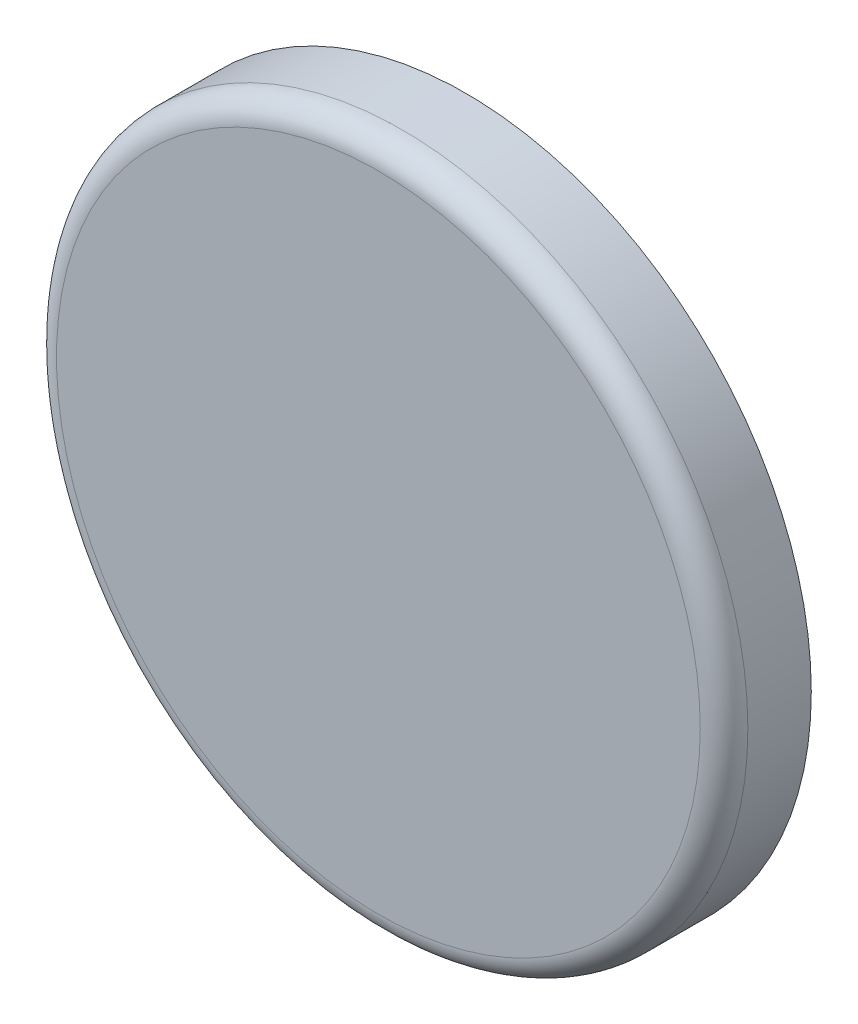
SolidWorks part; units mm, degrees
ref_plane "Alzado" through (0, 0, 0) normal (0, 0, 1) x (1, 0, 0)
ref_plane "Planta" through (0, 0, 0) normal (0, 1, 0) x (1, 0, 0)
ref_plane "Vista lateral" through (0, 0, 0) normal (1, 0, 0) x (0, 0, -1)
sketch "Croquis1" plane through (0, 0, 0) normal (0, 0, 1) x (1, 0, 0)
  line L0 (-47, 47) -> (47, -47) construction
  line L1 (47, -47) -> (47, 47) construction
  line L2 (47, 47) -> (-47, -47) construction
  circle A0 centre (0, 0) radius 43.5902
extrude "Saliente-Extruir1" add sketch "Croquis1" along normal blind 11
fillet "Redondeo1" radius 3 1 edges at (43.5902, 0, 11)
sketch "Croquis2" plane through (0, 0, 0) normal (0, 0, -1) x (-1, 0, 0)
  circle A0 centre (0, 0) radius 5.875
  dimension "D1" = 11.75
extrude "Cortar-Extruir1" cut sketch "Croquis2" against normal blind 9
sketch "Croquis3" plane through (0, 0, 0) normal (0, 0, -1) x (-1, 0, 0)
  circle A0 centre (0, 0) radius 7
  dimension "D1" = 14
extrude "Cortar-Extruir2" cut sketch "Croquis3" against normal blind 4.5
